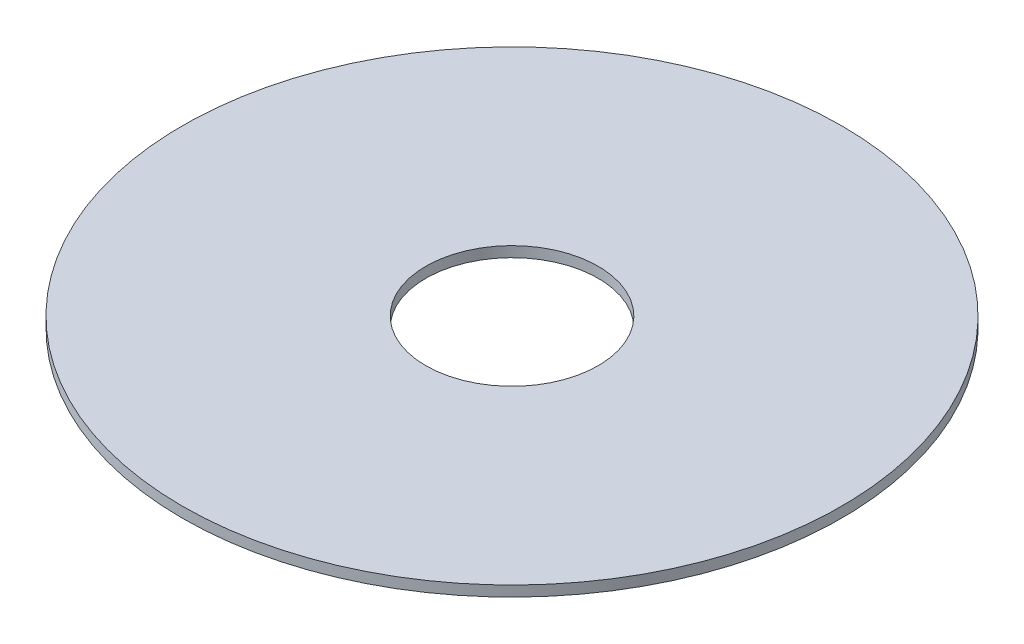
SolidWorks part; units mm, degrees
ref_plane "Front Plane" through (0, 0, 0) normal (0, 0, 1) x (1, 0, 0)
ref_plane "Top Plane" through (0, 0, 0) normal (0, 1, 0) x (1, 0, 0)
ref_plane "Right Plane" through (0, 0, 0) normal (1, 0, 0) x (0, 0, -1)
sketch "Sketch1" plane through (0, 0, 0) normal (0, 1, 0) x (1, 0, 0)
  circle A0 centre (0, 0) radius 53.5344
  circle A1 centre (0, 0) radius 14
extrude "Boss-Extrude1" add sketch "Sketch1" along normal blind 1.7
scale "Scale1" scale about centroid uniform scaling yes scale factor 0.5
